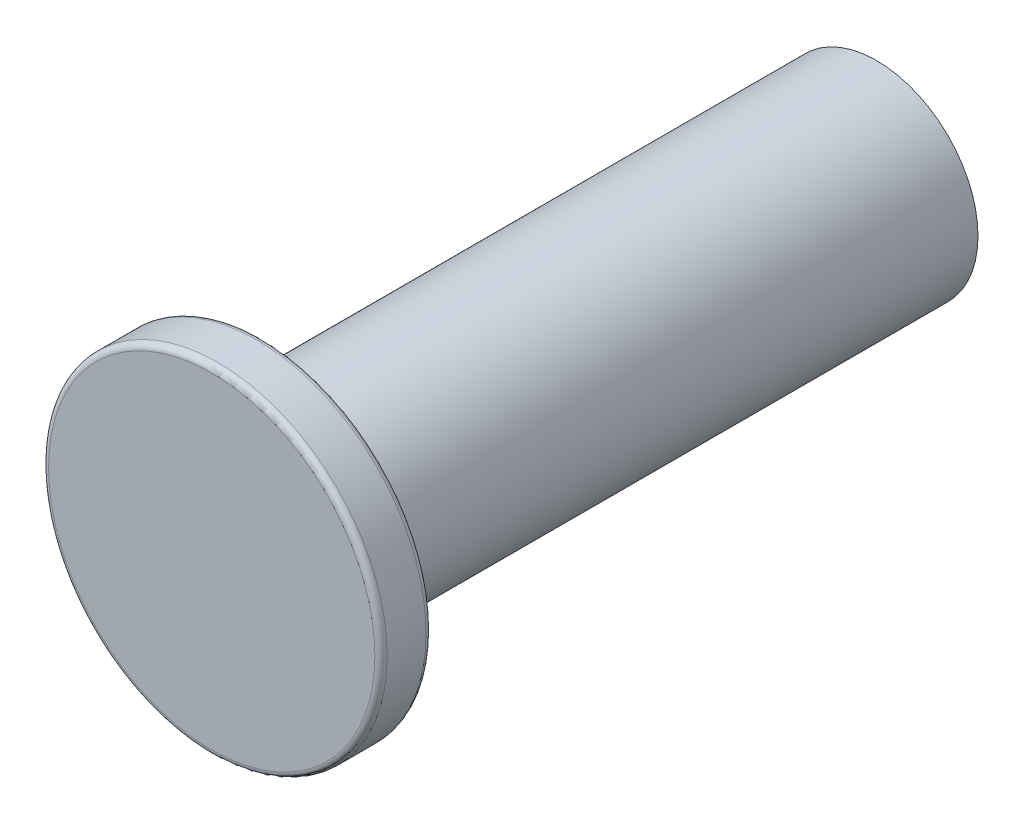
SolidWorks part; units mm, degrees
ref_plane "Front Plane" through (0, 0, 0) normal (0, 0, 1) x (1, 0, 0)
ref_plane "Top Plane" through (0, 0, 0) normal (0, 1, 0) x (1, 0, 0)
ref_plane "Right Plane" through (0, 0, 0) normal (1, 0, 0) x (0, 0, -1)
sketch "Sketch1" plane through (0, 0, 0) normal (0, 0, 1) x (1, 0, 0)
  circle A0 centre (0, 0) radius 12.573
  dimension "D1" = 25.146
extrude "Boss-Extrude1" add sketch "Sketch1" against normal blind 76.2
sketch "Sketch2" plane through (0, 0, 0) normal (0, 0, 1) x (1, 0, 0)
  circle A0 centre (0, 0) radius 21.0185
  dimension "D1" = 42.037
extrude "Boss-Extrude2" add sketch "Sketch2" along normal blind 6.35
fillet "Fillet1" radius 0.762 2 edges at (21.0185, 0, 6.35) (21.0185, 0, 0)
